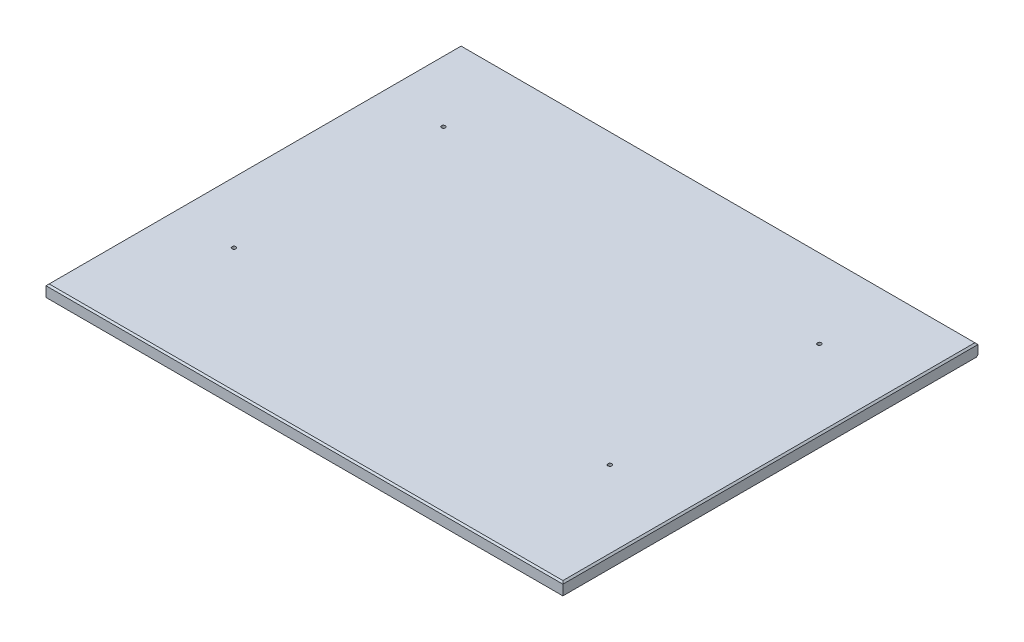
SolidWorks part; units mm, degrees
material "Oak"
ref_plane "Front Plane" through (0, 0, 0) normal (0, 0, 1) x (1, 0, 0)
ref_plane "Top Plane" through (0, 0, 0) normal (0, 1, 0) x (1, 0, 0)
ref_plane "Right Plane" through (0, 0, 0) normal (1, 0, 0) x (0, 0, -1)
sketch "Sketch1" plane through (0, 0, 0) normal (0, 1, 0) x (1, 0, 0)
  line L1 (0, 0) -> (838.2, 0)
  line L2 (0, 0) -> (0, 673.1)
  line L3 (0, 673.1) -> (838.2, 673.1)
  line L4 (838.2, 0) -> (838.2, 673.1)
  dimension "D1" = 673.1
  dimension "D2" = 838.2
extrude "Boss-Extrude1" add sketch "Sketch1" along normal blind 19.05
chamfer "Chamfer1" distance 2.54 angle 45 4 edges at (419.1, 19.05, -673.1) (838.2, 19.05, -336.55) (419.1, 19.05, 0) (0, 19.05, -336.55)
chamfer "Chamfer2" distance 2.54 angle 45 1 edges at (419.1, 0, -673.1)
sketch "Sketch2" plane through (0, 19.05, 0) normal (0, 1, 0) x (1, 0, 0)
  line L1 (101.6, 542.925) -> (711.2, 542.925) construction
  line L2 (101.6, 542.925) -> (101.6, 203.2) construction
  line L3 (101.6, 203.2) -> (711.2, 203.2) construction
  line L4 (711.2, 542.925) -> (711.2, 203.2) construction
  circle A1 centre (101.6, 542.925) radius 3.175
  circle A3 centre (101.6, 203.2) radius 3.175
  circle A5 centre (711.2, 542.925) radius 3.175
  circle A7 centre (711.2, 203.2) radius 3.175
  dimension "D1" = 6.35
  dimension "D2" = 609.6
  dimension "D3" = 339.725
  dimension "D4" = 203.2
  dimension "D5" = 101.6
extrude "Cut-Extrude1" cut sketch "Sketch2" against normal through all
